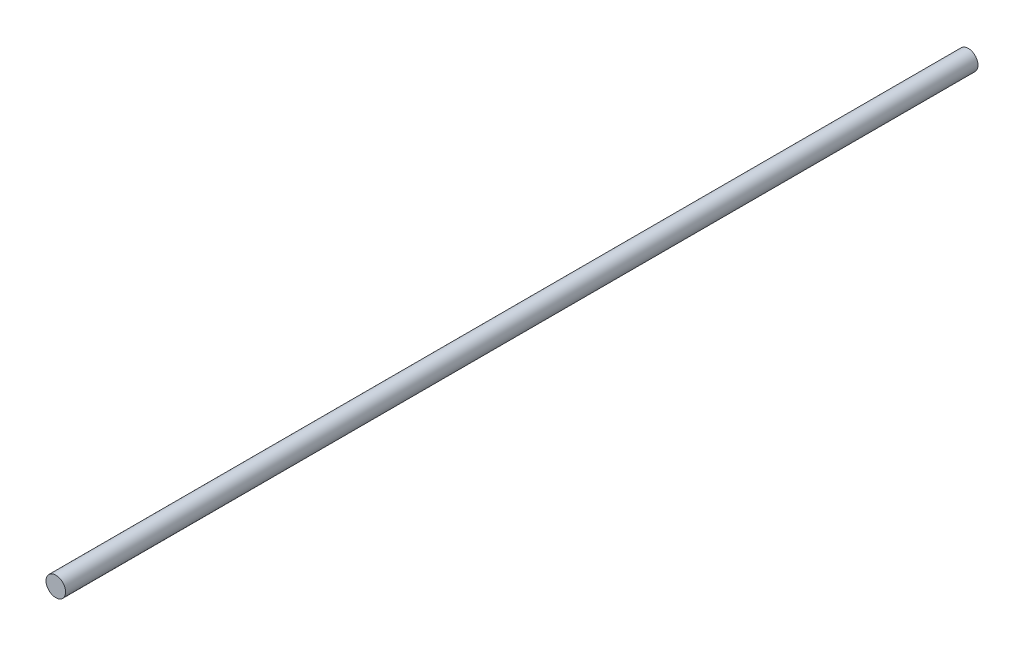
SolidWorks part; units mm, degrees
material "1.4000 (X6Cr13)"
ref_plane "Plan de face" through (0, 0, 0) normal (0, 0, 1) x (1, 0, 0)
ref_plane "Plan de dessus" through (0, 0, 0) normal (0, 1, 0) x (1, 0, 0)
ref_plane "Plan de droite" through (0, 0, 0) normal (1, 0, 0) x (0, 0, -1)
sketch "Esquisse1" plane through (0, 0, 0) normal (0, 0, 1) x (1, 0, 0)
  circle A0 centre (0, 0) radius 3
extrude "Boss.-Extru.1" add sketch "Esquisse1" along normal up to surface (251.0725 mm away) and the other way up to surface (28.9275 mm away)
